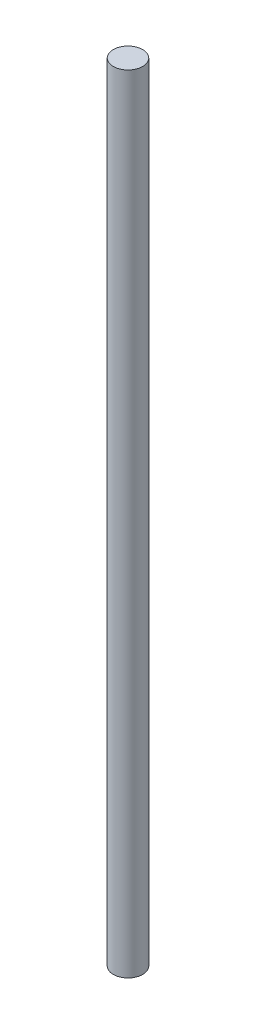
SolidWorks part; units mm, degrees
ref_plane "Front Plane" through (0, 0, 0) normal (0, 0, 1) x (1, 0, 0)
ref_plane "Top Plane" through (0, 0, 0) normal (0, 1, 0) x (1, 0, 0)
ref_plane "Right Plane" through (0, 0, 0) normal (1, 0, 0) x (0, 0, -1)
sketch "Sketch1" plane through (0, 0, 0) normal (0, 1, 0) x (1, 0, 0)
  circle A0 centre (0, 0) radius 6
  dimension "D1" = 12
extrude "Boss-Extrude1" add sketch "Sketch1" along normal blind 321
